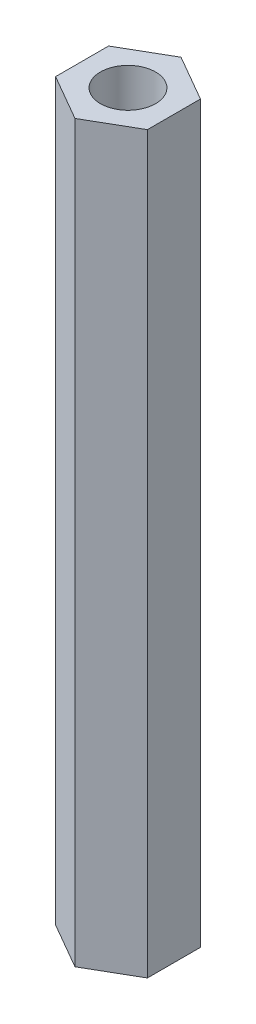
SolidWorks part; units mm, degrees
ref_plane "前基準面" through (0, 0, 0) normal (0, 0, 1) x (1, 0, 0)
ref_plane "上基準面" through (0, 0, 0) normal (0, 1, 0) x (1, 0, 0)
ref_plane "右基準面" through (0, 0, 0) normal (1, 0, 0) x (0, 0, -1)
sketch "草圖1" plane through (0, 0, 0) normal (0, 1, 0) x (1, 0, 0)
  line L0 (0, -5.1664) -> (0, 5.1664) construction
  line L1 (0, 2.8868) -> (-2.5, 1.4434)
  line L2 (-2.5, 1.4434) -> (-2.5, -1.4434)
  line L3 (-2.5, -1.4434) -> (0, -2.8868)
  line L4 (0, -2.8868) -> (2.5, -1.4434)
  line L5 (2.5, -1.4434) -> (2.5, 1.4434)
  line L6 (2.5, 1.4434) -> (0, 2.8868)
  circle A0 centre (0, 0) radius 1.5
  circle A1 centre (0, 0) radius 2.5 construction
  point P16 (0, 0)
  dimension "D1" = 3
  dimension "D2" = 5
extrude "填料-伸長1" add sketch "草圖1" along normal blind 40
